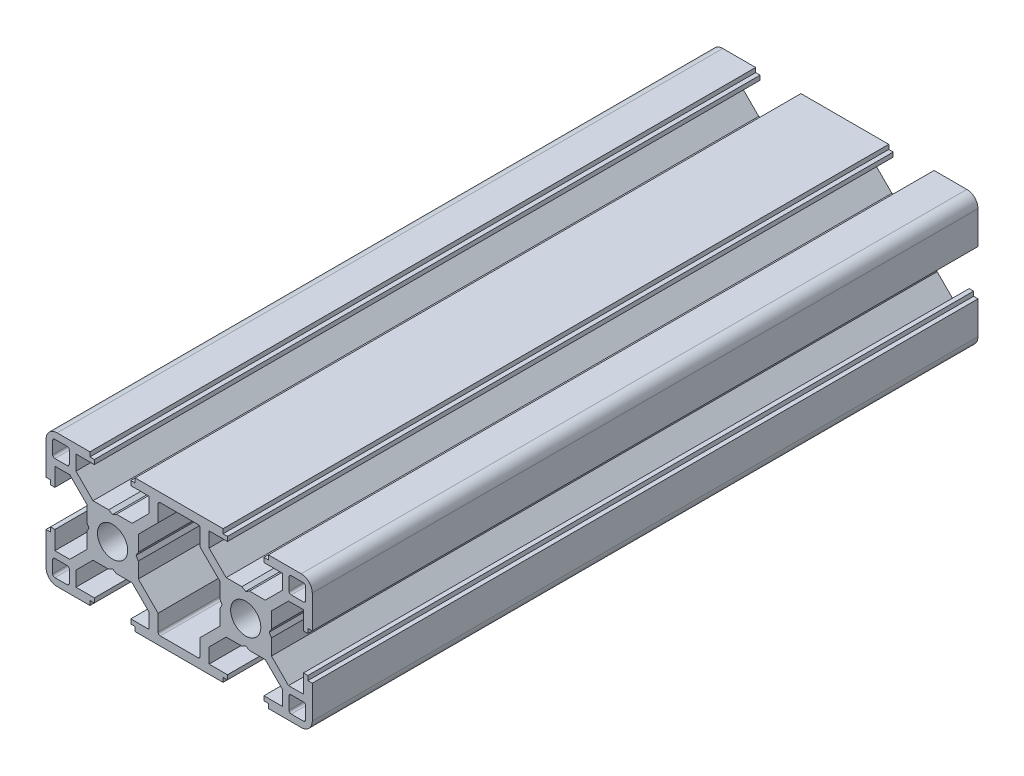
SolidWorks part; units mm, degrees
material "6063-T5"
ref_plane "Plan de face" through (0, 0, 0) normal (0, 0, 1) x (1, 0, 0)
ref_plane "Plan de dessus" through (0, 0, 0) normal (0, 1, 0) x (1, 0, 0)
ref_plane "Plan de droite" through (0, 0, 0) normal (1, 0, 0) x (0, 0, -1)
sketch "Esquisse1" plane through (0, 0, 0) normal (0, 0, 1) x (1, 0, 0)
  line L0 (16.032, 18.6935) -> (15.032, 18.6935)
  line L1 (15.032, 18.6935) -> (15.032, 19.6935)
  line L2 (16.032, 17.6935) -> (16.032, 18.6935)
  line L3 (-4.768, 19.6935) -> (15.032, 19.6935)
  line L4 (16.032, 17.6935) -> (11.882, 17.6935)
  line L5 (-4.768, 18.6935) -> (-4.768, 19.6935)
  line L6 (11.882, 14.3399) -> (11.882, 17.6935)
  line L7 (-5.768, 18.6935) -> (-4.768, 18.6935)
  line L8 (11.882, 14.3399) -> (15.7285, 10.4935)
  line L9 (-5.768, 17.6935) -> (-5.768, 18.6935)
  line L10 (19.266, 10.4935) -> (15.7285, 10.4935)
  line L11 (-5.768, 17.6935) -> (-1.618, 17.6935)
  line L12 (19.266, 10.4935) -> (20.132, 9.9935)
  line L13 (-1.618, 14.3399) -> (-1.618, 17.6935)
  line L14 (20.9981, 10.4935) -> (20.132, 9.9935)
  line L15 (-1.618, 14.3399) -> (-5.4644, 10.4935)
  line L16 (24.5356, 10.4935) -> (20.9981, 10.4935)
  line L17 (-9.0019, 10.4935) -> (-5.4644, 10.4935)
  line L18 (28.382, 14.3399) -> (24.5356, 10.4935)
  line L19 (-9.0019, 10.4935) -> (-9.868, 9.9935)
  line L20 (28.382, 14.3399) -> (28.382, 17.6935)
  line L21 (-10.734, 10.4935) -> (-9.868, 9.9935)
  line L22 (28.382, 17.6935) -> (24.232, 17.6935)
  line L23 (-14.2715, 10.4935) -> (-10.734, 10.4935)
  line L24 (24.232, 17.6935) -> (24.232, 18.6935)
  line L25 (-18.118, 14.3399) -> (-14.2715, 10.4935)
  line L26 (25.232, 18.6935) -> (24.232, 18.6935)
  line L27 (-18.118, 14.3399) -> (-18.118, 17.6935)
  line L28 (25.232, 18.6935) -> (25.232, 19.6935)
  line L29 (-18.118, 17.6935) -> (-13.968, 17.6935)
  line L30 (25.232, 19.6935) -> (32.632, 19.6935)
  line L31 (-13.968, 17.6935) -> (-13.968, 18.6935)
  line L32 (-14.968, 18.6935) -> (-13.968, 18.6935)
  line L33 (35.132, 17.1935) -> (35.132, 9.7935)
  line L34 (-14.968, 18.6935) -> (-14.968, 19.6935)
  line L35 (34.132, 9.7935) -> (35.132, 9.7935)
  line L36 (-22.368, 19.6935) -> (-14.968, 19.6935)
  line L37 (34.132, 8.7935) -> (34.132, 9.7935)
  line L38 (33.132, 8.7935) -> (34.132, 8.7935)
  line L39 (-24.868, 17.1935) -> (-24.868, 9.7935)
  line L40 (33.132, 8.7935) -> (33.132, 12.9435)
  line L41 (-23.868, 9.7935) -> (-24.868, 9.7935)
  line L42 (29.7785, 12.9435) -> (33.132, 12.9435)
  line L43 (-23.868, 8.7935) -> (-23.868, 9.7935)
  line L44 (29.7785, 12.9435) -> (25.932, 9.097)
  line L45 (-22.868, 8.7935) -> (-23.868, 8.7935)
  line L46 (25.932, 5.5595) -> (25.932, 9.097)
  line L47 (-22.868, 8.7935) -> (-22.868, 12.9435)
  line L48 (25.932, 5.5595) -> (25.432, 4.6935)
  line L49 (-19.5144, 12.9435) -> (-22.868, 12.9435)
  line L50 (25.932, 3.8275) -> (25.432, 4.6935)
  line L51 (-19.5144, 12.9435) -> (-15.668, 9.097)
  line L52 (25.932, 0.2899) -> (25.932, 3.8275)
  line L53 (-15.668, 5.5595) -> (-15.668, 9.097)
  line L54 (29.7785, -3.5565) -> (25.932, 0.2899)
  line L55 (-15.668, 5.5595) -> (-15.168, 4.6935)
  line L56 (29.7785, -3.5565) -> (33.132, -3.5565)
  line L57 (-15.668, 3.8275) -> (-15.168, 4.6935)
  line L58 (33.132, -3.5565) -> (33.132, 0.5935)
  line L59 (-15.668, 0.2899) -> (-15.668, 3.8275)
  line L60 (33.132, 0.5935) -> (34.132, 0.5935)
  line L61 (-19.5144, -3.5565) -> (-15.668, 0.2899)
  line L62 (34.132, -0.4065) -> (34.132, 0.5935)
  line L63 (-19.5144, -3.5565) -> (-22.868, -3.5565)
  line L64 (34.132, -0.4065) -> (35.132, -0.4065)
  line L65 (-22.868, -3.5565) -> (-22.868, 0.5935)
  line L66 (35.132, -0.4065) -> (35.132, -7.8065)
  line L67 (-22.868, 0.5935) -> (-23.868, 0.5935)
  line L68 (-23.868, -0.4065) -> (-23.868, 0.5935)
  line L69 (25.232, -10.3065) -> (32.632, -10.3065)
  line L70 (-23.868, -0.4065) -> (-24.868, -0.4065)
  line L71 (25.232, -9.3065) -> (25.232, -10.3065)
  line L72 (-24.868, -0.4065) -> (-24.868, -7.8065)
  line L73 (25.232, -9.3065) -> (24.232, -9.3065)
  line L74 (24.232, -8.3065) -> (24.232, -9.3065)
  line L75 (-22.368, -10.3065) -> (-14.968, -10.3065)
  line L76 (28.382, -8.3065) -> (24.232, -8.3065)
  line L77 (-14.968, -9.3065) -> (-14.968, -10.3065)
  line L78 (28.382, -4.953) -> (28.382, -8.3065)
  line L79 (-14.968, -9.3065) -> (-13.968, -9.3065)
  line L80 (28.382, -4.953) -> (24.5356, -1.1065)
  line L81 (-13.968, -8.3065) -> (-13.968, -9.3065)
  line L82 (24.5356, -1.1065) -> (20.9981, -1.1065)
  line L83 (-18.118, -8.3065) -> (-13.968, -8.3065)
  line L84 (20.9981, -1.1065) -> (20.132, -0.6065)
  line L85 (-18.118, -4.953) -> (-18.118, -8.3065)
  line L86 (19.266, -1.1065) -> (20.132, -0.6065)
  line L87 (-18.118, -4.953) -> (-14.2715, -1.1065)
  line L88 (19.266, -1.1065) -> (15.7285, -1.1065)
  line L89 (-14.2715, -1.1065) -> (-10.734, -1.1065)
  line L90 (11.882, -4.953) -> (15.7285, -1.1065)
  line L91 (-10.734, -1.1065) -> (-9.868, -0.6065)
  line L92 (11.882, -4.953) -> (11.882, -8.3065)
  line L93 (-9.0019, -1.1065) -> (-9.868, -0.6065)
  line L94 (16.032, -8.3065) -> (11.882, -8.3065)
  line L95 (-9.0019, -1.1065) -> (-5.4644, -1.1065)
  line L96 (16.032, -8.3065) -> (16.032, -9.3065)
  line L97 (-1.618, -4.953) -> (-5.4644, -1.1065)
  line L98 (16.032, -9.3065) -> (15.032, -9.3065)
  line L99 (-1.618, -4.953) -> (-1.618, -8.3065)
  line L100 (15.032, -9.3065) -> (15.032, -10.3065)
  line L101 (-5.768, -8.3065) -> (-1.618, -8.3065)
  line L102 (-4.768, -10.3065) -> (15.032, -10.3065)
  line L103 (-5.768, -8.3065) -> (-5.768, -9.3065)
  line L104 (-4.768, -9.3065) -> (-4.768, -10.3065)
  line L105 (-5.768, -9.3065) -> (-4.768, -9.3065)
  line L106 (-23.368, 14.9435) -> (-23.368, 17.6935)
  line L107 (-22.868, 18.1935) -> (-20.118, 18.1935)
  line L108 (-20.118, 14.4435) -> (-22.868, 14.4435)
  line L109 (-19.618, 17.6935) -> (-19.618, 14.9435)
  line L110 (-19.618, -5.5565) -> (-19.618, -8.3065)
  line L111 (-20.118, -8.8065) -> (-22.868, -8.8065)
  line L112 (-22.868, -5.0565) -> (-20.118, -5.0565)
  line L113 (-23.368, -8.3065) -> (-23.368, -5.5565)
  line L114 (14.332, 0.3255) -> (9.882, -4.1245)
  line L115 (9.882, -4.1245) -> (9.882, -7.8065)
  line L116 (14.332, 3.8275) -> (14.332, 0.3255)
  line L117 (14.832, 4.6935) -> (14.332, 3.8275)
  line L118 (9.382, -8.3065) -> (0.882, -8.3065)
  line L119 (14.332, 5.5595) -> (14.832, 4.6935)
  line L120 (14.332, 9.0615) -> (14.332, 5.5595)
  line L121 (0.382, -7.8065) -> (0.382, -4.1245)
  line L122 (9.882, 13.5115) -> (14.332, 9.0615)
  line L123 (0.382, -4.1245) -> (-4.068, 0.3255)
  line L124 (9.882, 17.1935) -> (9.882, 13.5115)
  line L125 (-4.068, 0.3255) -> (-4.068, 3.8275)
  line L126 (-4.068, 3.8275) -> (-4.568, 4.6935)
  line L127 (0.882, 17.6935) -> (9.382, 17.6935)
  line L128 (-4.568, 4.6935) -> (-4.068, 5.5595)
  line L129 (-4.068, 5.5595) -> (-4.068, 9.0615)
  line L130 (0.382, 13.5115) -> (0.382, 17.1935)
  line L131 (-4.068, 9.0615) -> (0.382, 13.5115)
  line L132 (29.882, 14.9435) -> (29.882, 17.6935)
  line L133 (30.382, 18.1935) -> (33.132, 18.1935)
  line L134 (33.132, 14.4435) -> (30.382, 14.4435)
  line L135 (33.632, 17.6935) -> (33.632, 14.9435)
  line L136 (29.882, -8.3065) -> (29.882, -5.5565)
  line L137 (30.382, -5.0565) -> (33.132, -5.0565)
  line L138 (33.132, -8.8065) -> (30.382, -8.8065)
  line L139 (33.632, -5.5565) -> (33.632, -8.3065)
  arc A0 (35.132, 17.1935) -> (32.632, 19.6935) centre (32.632, 17.1935) ccw
  arc A1 (-22.368, 19.6935) -> (-24.868, 17.1935) centre (-22.368, 17.1935) ccw
  arc A2 (32.632, -10.3065) -> (35.132, -7.8065) centre (32.632, -7.8065) ccw
  arc A3 (-24.868, -7.8065) -> (-22.368, -10.3065) centre (-22.368, -7.8065) ccw
  arc A4 (-22.868, 18.1935) -> (-23.368, 17.6935) centre (-22.868, 17.6935) ccw
  arc A5 (-23.368, 14.9435) -> (-22.868, 14.4435) centre (-22.868, 14.9435) ccw
  arc A6 (-19.618, 17.6935) -> (-20.118, 18.1935) centre (-20.118, 17.6935) ccw
  arc A7 (-20.118, 14.4435) -> (-19.618, 14.9435) centre (-20.118, 14.9435) ccw
  arc A8 (-20.118, -8.8065) -> (-19.618, -8.3065) centre (-20.118, -8.3065) ccw
  arc A9 (-19.618, -5.5565) -> (-20.118, -5.0565) centre (-20.118, -5.5565) ccw
  arc A10 (-23.368, -8.3065) -> (-22.868, -8.8065) centre (-22.868, -8.3065) ccw
  arc A11 (-22.868, -5.0565) -> (-23.368, -5.5565) centre (-22.868, -5.5565) ccw
  circle A12 centre (-9.868, 4.6935) radius 3.4
  arc A13 (9.382, -8.3065) -> (9.882, -7.8065) centre (9.382, -7.8065) ccw
  arc A14 (0.382, -7.8065) -> (0.882, -8.3065) centre (0.882, -7.8065) ccw
  arc A15 (9.882, 17.1935) -> (9.382, 17.6935) centre (9.382, 17.1935) ccw
  arc A16 (0.882, 17.6935) -> (0.382, 17.1935) centre (0.882, 17.1935) ccw
  circle A17 centre (20.132, 4.6935) radius 3.4
  arc A18 (30.382, 18.1935) -> (29.882, 17.6935) centre (30.382, 17.6935) ccw
  arc A19 (29.882, 14.9435) -> (30.382, 14.4435) centre (30.382, 14.9435) ccw
  arc A20 (33.632, 17.6935) -> (33.132, 18.1935) centre (33.132, 17.6935) ccw
  arc A21 (33.132, 14.4435) -> (33.632, 14.9435) centre (33.132, 14.9435) ccw
  arc A22 (30.382, -5.0565) -> (29.882, -5.5565) centre (30.382, -5.5565) ccw
  arc A23 (29.882, -8.3065) -> (30.382, -8.8065) centre (30.382, -8.3065) ccw
  arc A24 (33.632, -5.5565) -> (33.132, -5.0565) centre (33.132, -5.5565) ccw
  arc A25 (33.132, -8.8065) -> (33.632, -8.3065) centre (33.132, -8.3065) ccw
extrude "Extrusion1" add sketch "Esquisse1" along normal blind 150
